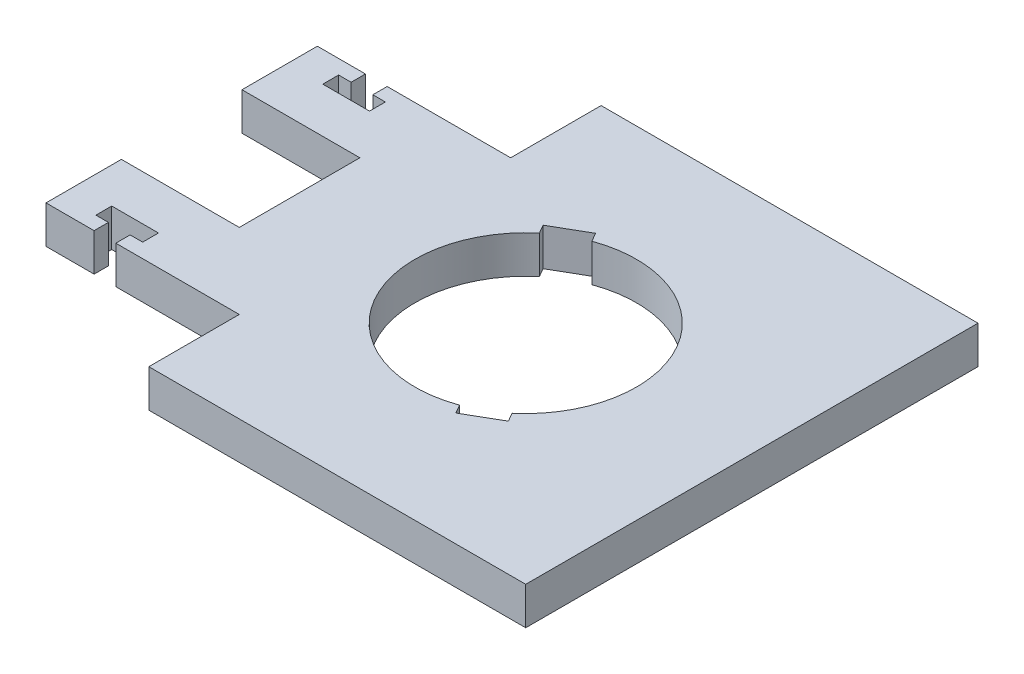
SolidWorks part; units mm, degrees
ref_plane "Front Plane" through (0, 0, 0) normal (0, 0, 1) x (1, 0, 0)
ref_plane "Top Plane" through (0, 0, 0) normal (0, 1, 0) x (1, 0, 0)
ref_plane "Right Plane" through (0, 0, 0) normal (1, 0, 0) x (0, 0, -1)
sketch "Sketch1" plane through (0, 0, 0) normal (0, 1, 0) x (1, 0, 0)
  line L0 (0, 0) -> (38.1, 0) construction
  line L1 (-25.4, -38.1) -> (38.1, -38.1)
  line L3 (-25.4, 38.1) -> (38.1, 38.1)
  line L4 (38.1, -38.1) -> (38.1, 38.1)
  line L5 (-38.1, -38.1) -> (38.1, 38.1) construction
  line L6 (-38.1, 38.1) -> (38.1, -38.1) construction
  line L7 (0, 0) -> (0, -18.5806) construction
  line L8 (9.2265, -15.9809) -> (10.033, -17.3776) construction
  line L11 (7.2271, -18.9976) -> (12.8389, -15.7576)
  line L12 (7.2271, -18.9976) -> (6.3819, -17.5338)
  line L14 (12.8389, -15.7576) -> (11.9937, -14.2938)
  line L15 (0, 0) -> (8.5457, 4.9338) construction
  line L17 (-7.2271, 18.9976) -> (-6.3819, 17.5338)
  line L18 (-12.8389, 15.7576) -> (-7.2271, 18.9976)
  line L19 (-12.8389, 15.7576) -> (-11.9937, 14.2938)
  line L21 (-38.1, -22.86) -> (-46.2026, -22.86)
  line L22 (-57.9628, -22.86) -> (-57.9628, -10.16)
  line L23 (-57.9628, -10.16) -> (-38.1, -10.16)
  line L24 (-38.1, 22.86) -> (-46.2026, 22.86)
  line L25 (-57.9628, 22.86) -> (-57.9628, 10.16)
  line L26 (-57.9628, 10.16) -> (-38.1, 10.16)
  line L28 (-38.1, -10.16) -> (-38.1, 10.16)
  line L29 (-48.0314, -24.13) -> (-48.0314, -17.78) construction
  line L30 (-51.9684, -17.78) -> (-44.0944, -17.78)
  line L31 (-44.0944, -17.78) -> (-44.0944, -20.447)
  line L32 (-44.0944, -20.447) -> (-46.2026, -20.447)
  line L33 (-46.2026, -20.447) -> (-46.2026, -22.86)
  line L34 (-49.8602, -20.447) -> (-49.8602, -22.86)
  line L35 (-51.9684, -20.447) -> (-49.8602, -20.447)
  line L36 (-51.9684, -17.78) -> (-51.9684, -20.447)
  line L37 (-49.8602, -22.86) -> (-57.9628, -22.86)
  line L38 (-51.9684, 20.447) -> (-49.8602, 20.447)
  line L39 (-49.8602, 20.447) -> (-49.8602, 22.86)
  line L40 (-46.2026, 20.447) -> (-46.2026, 22.86)
  line L41 (-44.0944, 20.447) -> (-46.2026, 20.447)
  line L42 (-44.0944, 17.78) -> (-44.0944, 20.447)
  line L43 (-51.9684, 17.78) -> (-44.0944, 17.78)
  line L44 (-51.9684, 17.78) -> (-51.9684, 20.447)
  line L45 (-49.8602, 22.86) -> (-57.9628, 22.86)
  line L46 (-38.1, -22.86) -> (-25.4, -22.86)
  line L47 (-25.4, -22.86) -> (-25.4, -38.1)
  line L48 (-25.4, 22.86) -> (-25.4, 38.1)
  line L49 (-38.1, 22.86) -> (-25.4, 22.86)
  arc A0 (11.9937, -14.2938) -> (-6.3819, 17.5338) centre (0, 0) ccw
  arc A1 (6.939, -17.0987) -> (11.3384, -14.5587) centre (0, 0) ccw construction
  arc A2 (6.939, -17.0987) -> (11.3384, -14.5587) centre (0, 0) ccw construction
  arc A3 (-11.9937, 14.2938) -> (6.3819, -17.5338) centre (0, 0) ccw
  point P0 (0, 0)
  point P11 (0, -18.5806)
  point P19 (10.033, -17.3776)
  point P25 (0, 0)
  point P35 (0, 0)
  dimension "D2" = 15.24
  dimension "D1" = 45
  dimension "D3" = 76.2
  dimension "D4" = 19.8628
  dimension "D5" = 20.32
  dimension "D6" = 7.874
  dimension "D7" = 5.08
  dimension "D8" = 2.667
  dimension "D9" = 3.6576
  dimension "D10" = 12.7
extrude "Boss-Extrude1" add sketch "Sketch1" against normal blind 6.35
